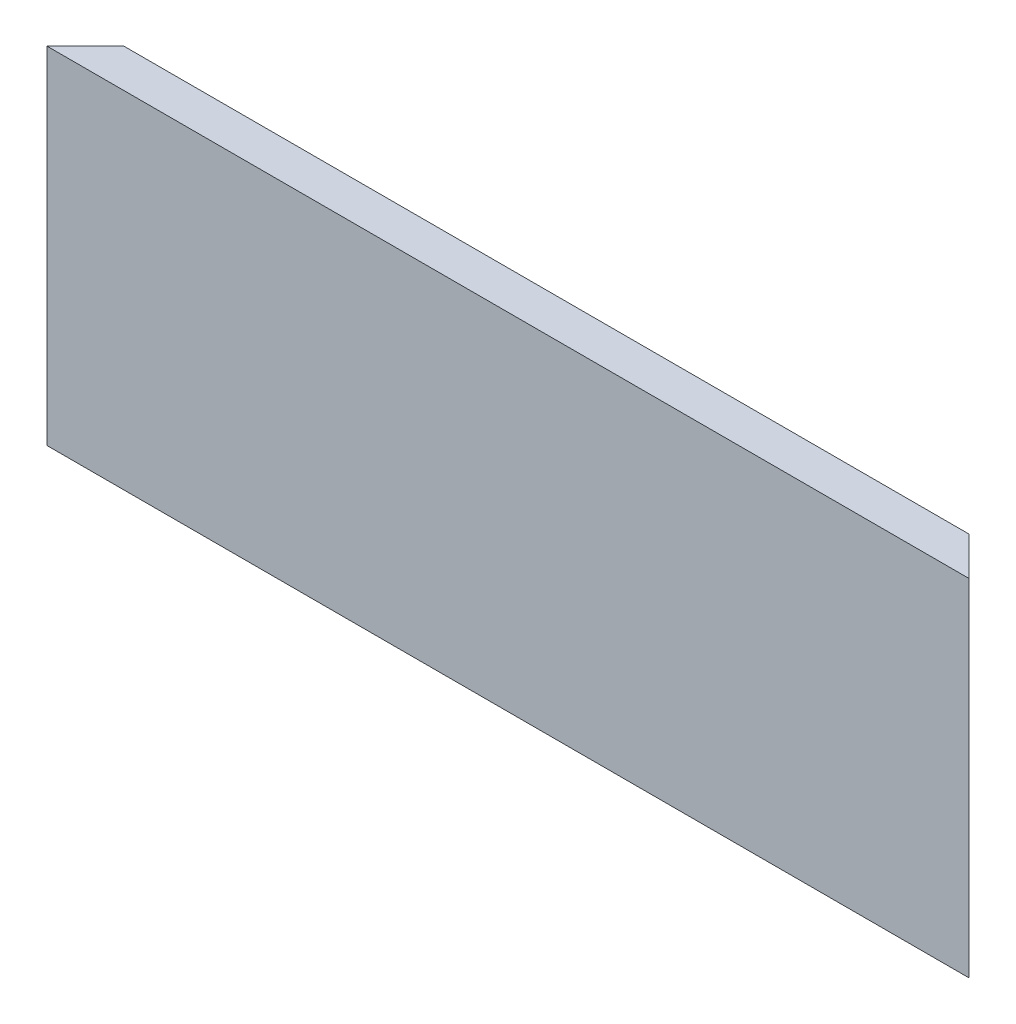
SolidWorks part; units mm, degrees
material "Beech"
ref_plane "Front Plane" through (0, 0, 0) normal (0, 0, 1) x (1, 0, 0)
ref_plane "Top Plane" through (0, 0, 0) normal (0, 1, 0) x (1, 0, 0)
ref_plane "Right Plane" through (0, 0, 0) normal (1, 0, 0) x (0, 0, -1)
other "Configuration Table"
sketch "Sketch1" plane through (0, 0, 0) normal (0, 0, 1) x (1, 0, 0)
  line L1 (0, 0) -> (152.4, 0)
  line L2 (0, 0) -> (0, 57.15)
  line L3 (0, 57.15) -> (152.4, 57.15)
  line L4 (152.4, 0) -> (152.4, 57.15)
  dimension "D1" = 57.15
  dimension "D2" = 152.4
extrude "Boss-Extrude1" add sketch "Sketch1" against normal blind 6.35
sketch "Sketch3" plane through (0, 57.15, 0) normal (0, 1, 0) x (1, 0, 0)
  line L0 (152.4, 0) -> (146.05, 6.35)
  line L1 (152.4, 6.35) -> (0, 6.35) construction
  line L2 (146.05, 6.35) -> (152.4, 6.35)
  line L3 (152.4, 6.35) -> (152.4, 0)
  line L4 (0, 0) -> (6.35, 6.35)
  line L5 (6.35, 6.35) -> (0, 6.35)
  line L6 (0, 6.35) -> (0, 0)
  dimension "D1" = 45
  dimension "D2" = 45
extrude "Cut-Extrude2" cut sketch "Sketch3" against normal through all
sketch "Sketch4" plane through (0, 0, 0) normal (1, 0, 0) x (0, 0, -1)
  line L0 (6.35, 46.355) -> (3.175, 46.355)
  line L1 (6.35, 0) -> (6.35, 57.15) construction
  line L2 (3.175, 46.355) -> (3.175, 41.5925)
  line L3 (3.175, 41.5925) -> (6.35, 41.5925)
  line L4 (6.35, 41.5925) -> (6.35, 46.355)
  line L5 (6.35, 57.15) -> (0, 57.15) construction
  dimension "D1" = 10.795
  dimension "D2" = 4.7625
  dimension "D3" = 3.175
extrude "Cut-Extrude3" cut sketch "Sketch4" along normal through all
sketch "Sketch5" plane through (0, 0, 0) normal (1, 0, 0) x (0, 0, -1)
  line L0 (6.35, 4.7625) -> (3.175, 4.7625)
  line L1 (6.35, 0) -> (6.35, 41.5925) construction
  line L2 (3.175, 4.7625) -> (3.175, 8.0137)
  line L3 (3.175, 8.0137) -> (6.35, 8.0137)
  line L4 (6.35, 8.0137) -> (6.35, 4.7625)
  line L5 (6.35, 0) -> (0, 0) construction
  dimension "D1" = 4.7625
  dimension "D2" = 3.175
  dimension "D3" = 3.2512
extrude "Cut-Extrude4" cut sketch "Sketch5" along normal through all
sketch "Sketch6" plane through (0, 0, -6.35) normal (0, 0, -1) x (-1, 0, 0)
  line L0 (-152.4, 0) -> (-152.4, 57.15) construction
  line L1 (-146.05, 57.15) -> (-6.35, 57.15) construction
  circle A0 centre (-142.748, 49.911) radius 2.3813
  dimension "D1" = 9.652
  dimension "D2" = 4.7625
  dimension "D3" = 7.239
extrude "Cut-Extrude5" cut sketch "Sketch6" against normal blind 5.08
